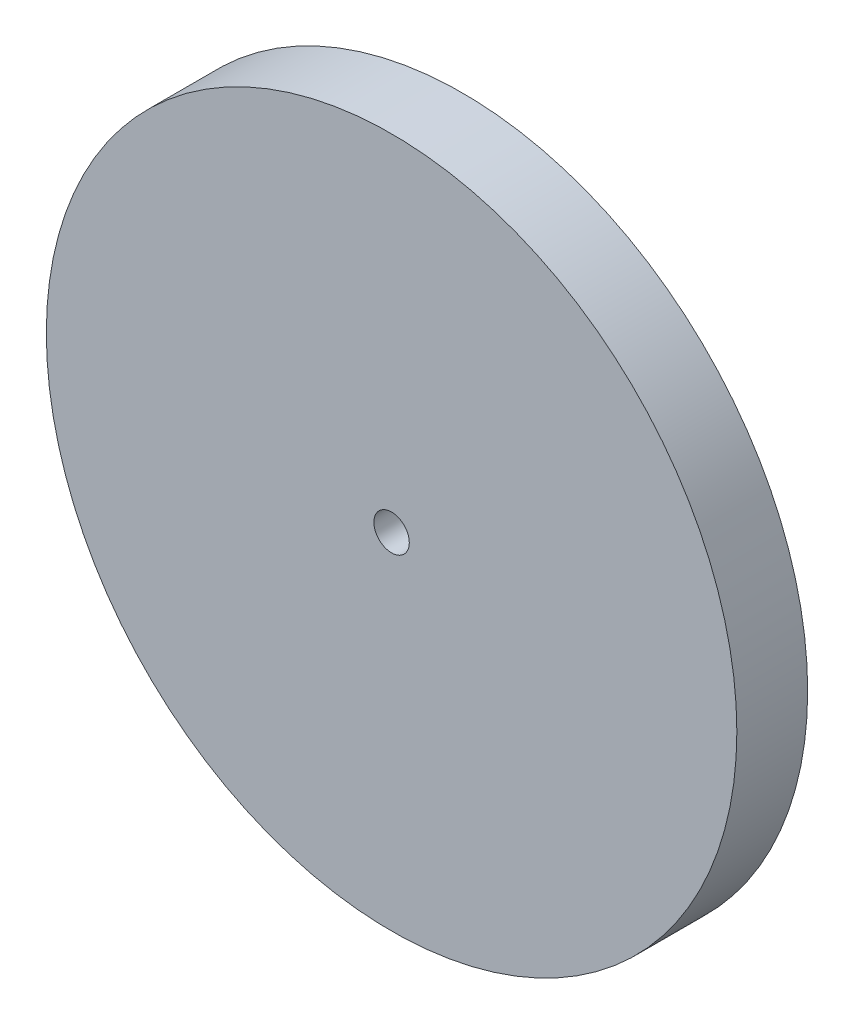
SolidWorks part; units mm, degrees
material "ABS"
ref_plane "前视基准面" through (0, 0, 0) normal (0, 0, 1) x (1, 0, 0)
ref_plane "上视基准面" through (0, 0, 0) normal (0, 1, 0) x (1, 0, 0)
ref_plane "右视基准面" through (0, 0, 0) normal (1, 0, 0) x (0, 0, -1)
other "Configuration Table"
sketch "草图1" plane through (0, 0, 0) normal (0, 0, 1) x (1, 0, 0)
  circle A0 centre (0, 0) radius 19.5
  dimension "D1" = 39
extrude "凸台-拉伸1" add sketch "草图1" along normal blind 4
sketch "草图2" plane through (0, 0, 4) normal (0, 0, 1) x (1, 0, 0)
  circle A0 centre (0, 0) radius 1
  dimension "D1" = 2
extrude "切除-拉伸1" cut sketch "草图2" against normal through all
